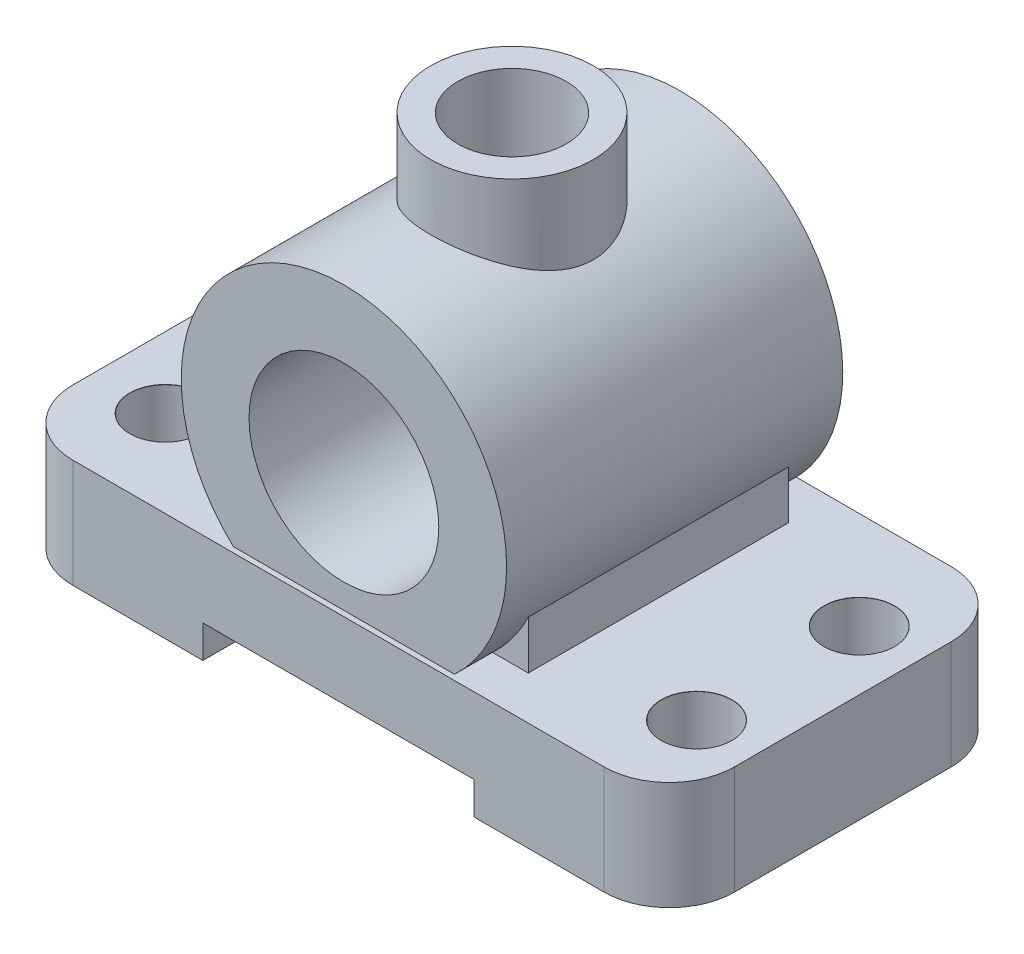
SolidWorks part; units mm, degrees
ref_plane "Спереди" through (0, 0, 0) normal (0, 0, 1) x (1, 0, 0)
ref_plane "Сверху" through (0, 0, 0) normal (0, 1, 0) x (1, 0, 0)
ref_plane "Справа" through (0, 0, 0) normal (1, 0, 0) x (0, 0, -1)
other "Configuration Table"
sketch "Эскиз12" plane through (0, 0, 0) normal (0, 1, 0) x (1, 0, 0)
  line L1 (-49, -32) -> (49, -32)
  line L2 (-61, -20) -> (-61, 20)
  line L3 (-49, 32) -> (49, 32)
  line L4 (61, -20) -> (61, 20)
  line L5 (-61, -32) -> (61, 32) construction
  line L6 (-61, 32) -> (61, -32) construction
  arc A0 (49, -32) -> (61, -20) centre (49, -20) ccw
  arc A1 (49, 32) -> (61, 20) centre (49, 20) cw
  arc A2 (-49, -32) -> (-61, -20) centre (-49, -20) cw
  arc A3 (-61, 20) -> (-49, 32) centre (-49, 20) cw
  point P0 (0, 0)
  dimension "D3" = 12
  dimension "D1" = 122
  dimension "D2" = 64
extrude "Бобышка-Вытянуть12" add sketch "Эскиз12" along normal blind 20
sketch "Эскиз13" plane through (0, 20, 0) normal (0, 1, 0) x (1, 0, 0)
  line L1 (27, -24) -> (-27, -24)
  line L2 (27, -24) -> (27, 24)
  line L3 (27, 24) -> (-27, 24)
  line L4 (-27, -24) -> (-27, 24)
  line L5 (27, -24) -> (-27, 24) construction
  line L6 (27, 24) -> (-27, -24) construction
  point P0 (0, 0)
  dimension "D1" = 54
  dimension "D2" = 48
extrude "Бобышка-Вытянуть13" add sketch "Эскиз13" along normal blind 22
sketch "Эскиз14" plane through (0, 0, 24) normal (0, 0, 1) x (1, 0, 0)
  line L0 (-49, 0) -> (49, 0) construction
  circle A0 centre (0, 42) radius 30
  dimension "D2" = 60
  dimension "D1" = 42
extrude "Бобышка-Вытянуть14" add sketch "Эскиз14" along normal blind 62 from offset 55 offset against normal yes
sketch "Эскиз19" plane through (0, 0, 32) normal (0, 0, 1) x (1, 0, 0)
  line L1 (25, -6) -> (-25, -6)
  line L2 (25, -6) -> (25, 6)
  line L3 (25, 6) -> (-25, 6)
  line L4 (-25, -6) -> (-25, 6)
  line L5 (25, -6) -> (-25, 6) construction
  line L6 (25, 6) -> (-25, -6) construction
  point P0 (0, 0)
  dimension "D1" = 50
  dimension "D2" = 12
extrude "Вырез-Вытянуть3" cut sketch "Эскиз19" against normal through all both
sketch "Эскиз20" plane through (0, 0, 0) normal (0, 1, 0) x (1, 0, 0)
  circle A0 centre (0, 0) radius 15
  dimension "D1" = 30
extrude "Бобышка-Вытянуть17" add sketch "Эскиз20" along normal blind 78 from surface at 6 starting at face at (0, 6, 0)
sketch "Эскиз21" plane through (0, 84, 0) normal (0, 1, 0) x (1, 0, 0)
  circle A0 centre (0, 0) radius 10
  dimension "D1" = 20
extrude "Вырез-Вытянуть4" cut sketch "Эскиз21" against normal through all both
sketch "Эскиз23" plane through (0, 0, 31) normal (0, 0, 1) x (1, 0, 0)
  circle A0 centre (0, 42) radius 17.5
  dimension "D1" = 35
extrude "Вырез-Вытянуть7" cut sketch "Эскиз23" against normal blind 48
sketch "Эскиз25" plane through (0, 0, -31) normal (0, 0, -1) x (-1, 0, 0)
  circle A0 centre (0, 42) radius 10
  dimension "D1" = 20
extrude "Вырез-Вытянуть8" cut sketch "Эскиз25" against normal blind 17
hole_wizard "Диаметр отверстия Ø13.0 (13)2" positions "Эскиз34" profile "Эскиз35" hole size "Ø13.0" standard "ISO" end condition through all
sketch "Эскиз34" plane through (0, 20, 0) normal (0, 1, 0) x (1, 0, 0)
  line L0 (30, 31) -> (-30, 31) construction
  point P0 (-47.9634, 14)
  point P2 (-47.9634, -16)
  point P4 (50.0366, -16)
  point P6 (50.0366, 14)
  point P11 (0, 0)
  dimension "D1" = 17
  dimension "D2" = 30
  dimension "D3" = 98
sketch "Эскиз35" plane through (-47.9634, 20, -14) normal (1, 0, 0) x (0, 0, 1)
  line L0 (0, 0) -> (0, 20)
  line L1 (0, 20) -> (6.5, 20)
  line L2 (6.5, 20) -> (6.5, 0.025)
  line L3 (6.5, 0.025) -> (6.525, 0)
  line L5 (6.525, 0) -> (0, 0)
  line L6 (-6.5, 0.025) -> (-6.525, 0) construction
  line L11 (0, -6.35) -> (0, 107.95) construction
  dimension "Диаметр сквозного отверстия" = 13
  dimension "Глубина сквозного отверстия" = 20
  dimension "Диаметр передней зенковки" = 13.05
  dimension "Угол передней зенковки" = 90
